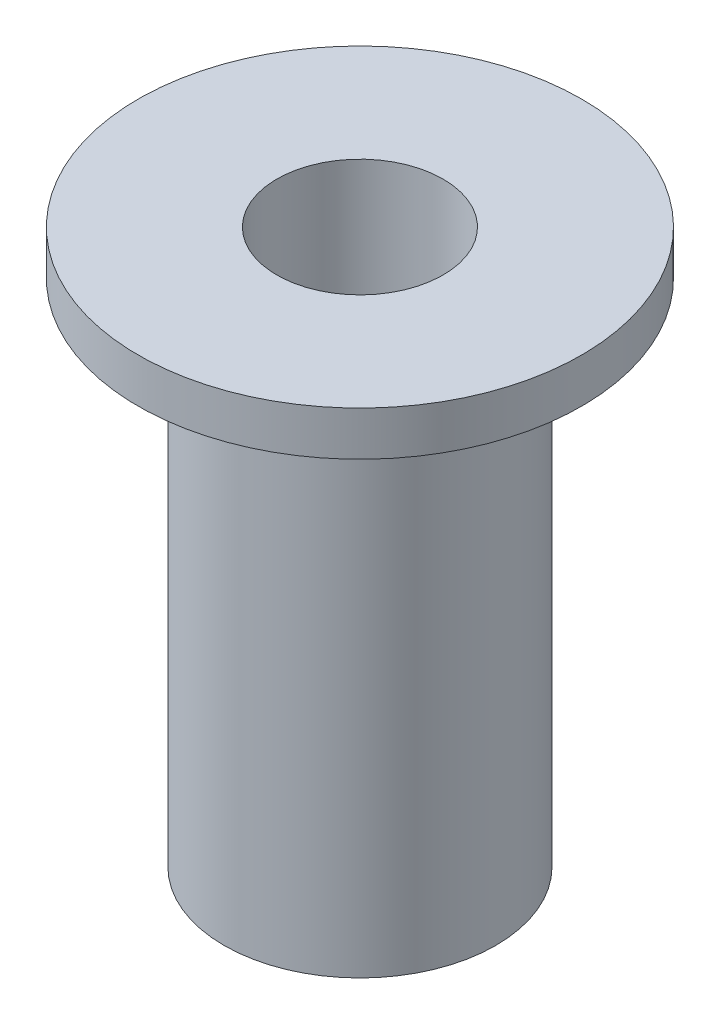
SolidWorks part; units mm, degrees
ref_plane "Front Plane" through (0, 0, 0) normal (0, 0, 1) x (1, 0, 0)
ref_plane "Top Plane" through (0, 0, 0) normal (0, 1, 0) x (1, 0, 0)
ref_plane "Right Plane" through (0, 0, 0) normal (1, 0, 0) x (0, 0, -1)
sketch "Sketch1" plane through (0, 0, 0) normal (0, 0, 1) x (1, 0, 0)
  line L0 (4, 10) -> (1.5, 10)
  line L1 (1.5, 10) -> (1.5, 0)
  line L2 (1.5, 0) -> (2.45, 0)
  line L3 (2.45, 0) -> (2.45, 9.2)
  line L4 (2.45, 9.2) -> (4, 9.2)
  line L5 (4, 9.2) -> (4, 10)
  line L6 (0, 0) -> (0, 2.6153) construction
  dimension "D1" = 4
  dimension "D2" = 0.8
  dimension "D3" = 1.5
  dimension "D4" = 2.45
  dimension "D5" = 10
revolve "Revolve1" add sketch "Sketch1" angle 360 about L6
